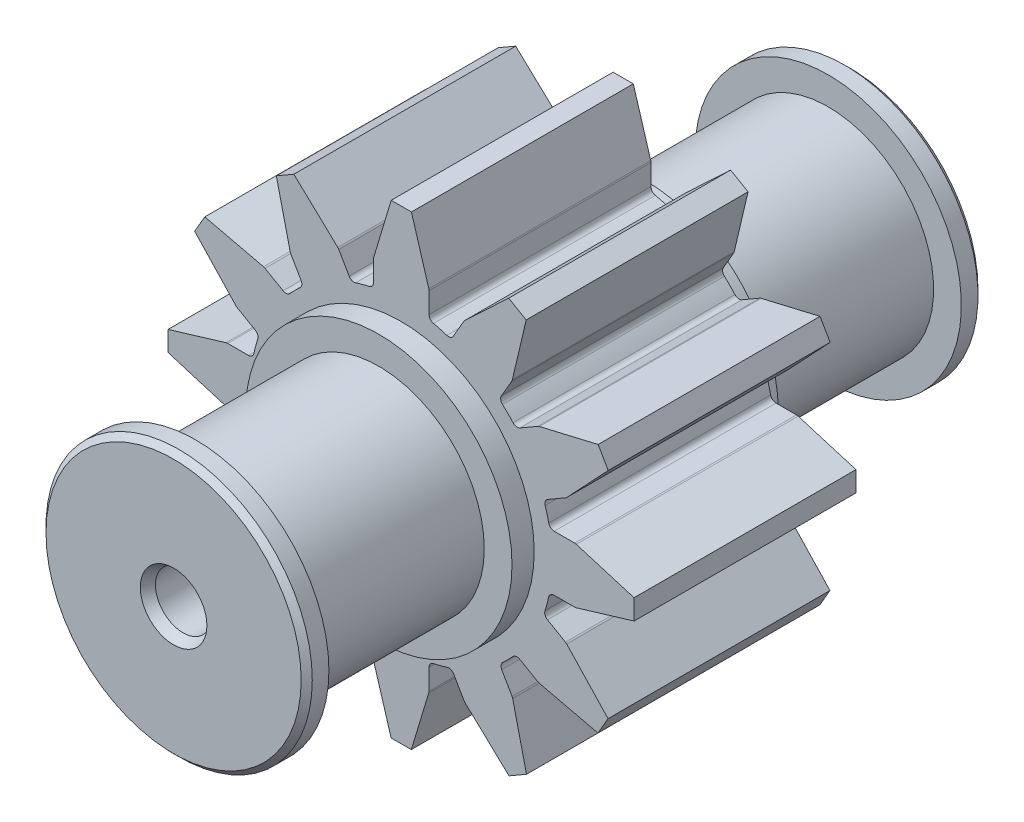
SolidWorks part; units mm, degrees
ref_plane "Спереди" through (0, 0, 0) normal (0, 0, 1) x (1, 0, 0)
ref_plane "Сверху" through (0, 0, 0) normal (0, 1, 0) x (1, 0, 0)
ref_plane "Справа" through (0, 0, 0) normal (1, 0, 0) x (0, 0, -1)
sketch "Эскиз2" plane through (0, 0, 0) normal (0, 0, 1) x (1, 0, 0)
  line L20 (53.7645, -2.946) -> (53.7645, -1.0771)
  line L21 (53.7433, -0.9329) -> (52.1747, 4.2742)
  line L22 (52.1747, 4.2742) -> (50.3546, 4.2742)
  line L23 (50.3546, 4.2742) -> (48.7858, -0.9329)
  line L24 (48.7645, -1.0772) -> (48.7645, -2.9531)
  line L27 (48.7555, -30.4797) -> (48.7555, -32.3473)
  line L28 (48.7768, -32.4916) -> (50.3453, -37.6987)
  line L29 (50.3453, -37.6987) -> (52.1655, -37.6987)
  line L30 (52.1655, -37.6987) -> (53.7343, -32.4916)
  line L31 (53.7555, -32.3473) -> (53.7555, -30.4775)
  line L34 (37.4896, -14.2638) -> (35.6099, -14.2638)
  line L36 (30.2415, -15.8598) -> (30.2586, -17.6738)
  line L37 (30.2586, -17.6738) -> (35.4657, -19.2426)
  line L38 (35.6099, -19.2638) -> (37.5151, -19.2638)
  line L39 (30.2415, -15.8598) -> (35.4656, -14.2851)
  line L41 (65.0289, -19.2139) -> (66.8888, -19.2139)
  line L42 (67.033, -19.1927) -> (72.2401, -17.6241)
  line L43 (72.2401, -17.6241) -> (72.2401, -15.8039)
  line L44 (72.2401, -15.8039) -> (67.033, -14.2352)
  line L45 (66.8887, -14.2139) -> (65.0384, -14.2141)
  line L48 (46.564, -3.5408) -> (45.6287, -1.9209)
  line L49 (45.5382, -1.8066) -> (41.5762, 1.9187)
  line L50 (41.5762, 1.9187) -> (39.9999, 1.0086)
  line L51 (39.9999, 1.0086) -> (41.2449, -4.2853)
  line L52 (41.2986, -4.4209) -> (42.233, -6.0394)
  line L55 (40.6086, -7.6603) -> (38.9805, -6.7203)
  line L56 (38.845, -6.6666) -> (33.5512, -5.4215)
  line L57 (33.5512, -5.4215) -> (32.6411, -6.9978)
  line L58 (32.6411, -6.9978) -> (36.3662, -10.9599)
  line L59 (36.4805, -11.0505) -> (38.0992, -11.985)
  line L62 (38.0961, -21.4251) -> (36.4775, -22.3596)
  line L63 (36.3633, -22.4501) -> (32.638, -26.4121)
  line L64 (32.638, -26.4121) -> (33.5481, -27.9884)
  line L65 (33.5481, -27.9884) -> (38.8378, -26.7444)
  line L66 (38.9806, -26.6864) -> (40.5573, -25.7405)
  line L67 (32.638, -26.4121) -> (36.4137, -22.3964)
  line L69 (42.2473, -27.4181) -> (41.3131, -29.0361)
  line L70 (41.2594, -29.1716) -> (40.0143, -34.4654)
  line L71 (40.0143, -34.4654) -> (41.5906, -35.3755)
  line L72 (41.5906, -35.3755) -> (45.553, -31.6502)
  line L73 (45.6432, -31.5364) -> (46.5897, -29.9013)
  line L76 (55.9807, -29.8805) -> (56.9183, -31.5045)
  line L77 (57.0088, -31.6188) -> (60.9708, -35.344)
  line L78 (60.9708, -35.344) -> (62.5471, -34.434)
  line L79 (62.5471, -34.434) -> (61.3021, -29.1401)
  line L80 (61.2484, -29.0045) -> (60.3134, -27.3849)
  line L83 (61.9386, -25.7577) -> (63.5568, -26.6919)
  line L84 (63.6923, -26.7456) -> (68.9861, -27.9908)
  line L85 (68.9861, -27.9908) -> (69.8962, -26.4145)
  line L86 (69.8962, -26.4145) -> (66.171, -22.4523)
  line L87 (66.0568, -22.3618) -> (64.4371, -21.4267)
  line L90 (64.4528, -12.024) -> (66.0728, -11.0887)
  line L91 (66.1871, -10.9982) -> (69.9123, -7.0362)
  line L92 (69.9123, -7.0362) -> (69.0022, -5.4599)
  line L93 (69.0022, -5.4599) -> (63.7083, -6.7049)
  line L94 (63.5728, -6.7586) -> (61.9545, -7.6929)
  line L97 (60.2872, -6.0251) -> (61.2186, -4.412)
  line L98 (61.2723, -4.2764) -> (62.5174, 1.0174)
  line L99 (62.5174, 1.0174) -> (60.9411, 1.9274)
  line L100 (60.9411, 1.9274) -> (56.979, -1.7977)
  line L101 (56.8884, -1.912) -> (55.9532, -3.5318)
  arc A0 (48.3706, -3.4418) -> (48.7645, -2.9531) centre (48.2645, -2.9531) ccw
  arc A1 (47.1481, -3.7675) -> (46.564, -3.5408) centre (46.997, -3.2908) cw
  arc A2 (48.3706, -3.4418) -> (47.1481, -3.7675) centre (51.2539, -16.7205) ccw
  arc A3 (54.1578, -3.4345) -> (55.3689, -3.7584) centre (51.2539, -16.7205) cw
  arc A4 (60.3845, -6.6456) -> (61.3338, -7.5955) centre (51.2539, -16.7205) cw
  arc A5 (64.2262, -12.6081) -> (64.5499, -13.8206) centre (51.2539, -16.7205) cw
  arc A6 (64.5403, -19.6077) -> (64.2107, -20.8421) centre (51.2539, -16.7205) cw
  arc A7 (61.3184, -25.8547) -> (60.4095, -26.7654) centre (51.2539, -16.7205) cw
  arc A8 (55.3952, -29.6543) -> (54.1489, -29.989) centre (51.2539, -16.7205) cw
  arc A9 (48.362, -29.9912) -> (47.1727, -29.6749) centre (51.2539, -16.7205) cw
  arc A10 (42.1495, -26.7971) -> (41.1853, -25.8337) centre (51.2539, -16.7205) cw
  arc A11 (38.3225, -20.8403) -> (38.0033, -19.6557) centre (51.2539, -16.7205) cw
  arc A12 (37.9785, -13.8689) -> (38.3253, -12.5708) centre (51.2539, -16.7205) cw
  arc A13 (41.2278, -7.5645) -> (42.1358, -6.6599) centre (51.2539, -16.7205) cw
  arc A14 (54.1578, -3.4345) -> (53.7645, -2.946) centre (54.2645, -2.946) cw
  arc A15 (55.3689, -3.7584) -> (55.9532, -3.5318) centre (55.5202, -3.2818) ccw
  arc A16 (60.3845, -6.6456) -> (60.2872, -6.0251) centre (60.7202, -6.2751) cw
  arc A17 (61.9545, -7.6929) -> (61.3338, -7.5955) centre (61.7045, -7.2599) cw
  arc A18 (56.979, -1.7977) -> (56.8884, -1.912) centre (57.3215, -2.162) ccw
  arc A19 (53.7433, -0.9329) -> (53.7645, -1.0771) centre (53.2645, -1.0771) cw
  arc A20 (48.7858, -0.9329) -> (48.7645, -1.0772) centre (49.2645, -1.0772) ccw
  arc A21 (45.5382, -1.8066) -> (45.6287, -1.9209) centre (45.1957, -2.1709) cw
  arc A22 (63.5728, -6.7586) -> (63.7083, -6.7049) centre (63.8228, -7.1916) cw
  arc A23 (61.2723, -4.2764) -> (61.2186, -4.412) centre (60.7856, -4.162) cw
  arc A24 (64.5499, -13.8206) -> (65.0384, -14.2141) centre (65.0384, -13.7141) ccw
  arc A25 (64.2262, -12.6081) -> (64.4528, -12.024) centre (64.7028, -12.457) cw
  arc A26 (66.8887, -14.2139) -> (67.033, -14.2352) centre (66.8888, -14.7139) cw
  arc A27 (66.1871, -10.9982) -> (66.0728, -11.0887) centre (65.8228, -10.6557) cw
  arc A28 (64.5403, -19.6077) -> (65.0289, -19.2139) centre (65.0289, -19.7139) cw
  arc A29 (67.033, -19.1927) -> (66.8888, -19.2139) centre (66.8888, -18.7139) cw
  arc A30 (64.4371, -21.4267) -> (64.2107, -20.8421) centre (64.6871, -20.9937) cw
  arc A31 (66.171, -22.4523) -> (66.0568, -22.3618) centre (65.8068, -22.7948) ccw
  arc A32 (61.3184, -25.8547) -> (61.9386, -25.7577) centre (61.6886, -26.1907) cw
  arc A33 (63.6923, -26.7456) -> (63.5568, -26.6919) centre (63.8068, -26.2589) cw
  arc A34 (60.3134, -27.3849) -> (60.4095, -26.7654) centre (60.7464, -27.1349) cw
  arc A35 (61.3021, -29.1401) -> (61.2484, -29.0045) centre (60.8154, -29.2545) ccw
  arc A36 (56.9183, -31.5045) -> (57.0088, -31.6188) centre (57.3513, -31.2545) ccw
  arc A37 (55.9807, -29.8805) -> (55.3952, -29.6543) centre (55.5477, -30.1305) ccw
  arc A38 (53.7555, -30.4775) -> (54.1489, -29.989) centre (54.2555, -30.4775) cw
  arc A39 (53.7343, -32.4916) -> (53.7555, -32.3473) centre (53.2555, -32.3473) ccw
  arc A40 (48.7555, -32.3473) -> (48.7768, -32.4916) centre (49.2555, -32.3473) ccw
  arc A41 (48.362, -29.9912) -> (48.7555, -30.4797) centre (48.2555, -30.4797) cw
  arc A42 (46.5897, -29.9013) -> (47.1727, -29.6749) centre (47.0224, -30.1518) cw
  arc A43 (45.553, -31.6502) -> (45.6432, -31.5364) centre (45.2105, -31.2859) ccw
  arc A44 (41.3131, -29.0361) -> (41.2594, -29.1716) centre (41.7462, -29.2861) ccw
  arc A45 (42.1495, -26.7971) -> (42.2473, -27.4181) centre (41.8143, -27.1681) cw
  arc A46 (41.1853, -25.8337) -> (40.5573, -25.7405) centre (40.8145, -26.1692) ccw
  arc A47 (38.8378, -26.7444) -> (38.9806, -26.6864) centre (38.7234, -26.2577) ccw
  arc A48 (36.4775, -22.3596) -> (36.3633, -22.4501) centre (36.7275, -22.7926) ccw
  arc A49 (38.0961, -21.4251) -> (38.3225, -20.8403) centre (37.8461, -20.9921) ccw
  arc A50 (37.5151, -19.2638) -> (38.0033, -19.6557) centre (37.5151, -19.7638) cw
  arc A51 (35.4657, -19.2426) -> (35.6099, -19.2638) centre (35.6099, -18.7638) ccw
  arc A52 (35.4656, -14.2851) -> (35.6099, -14.2638) centre (35.6099, -14.7638) cw
  arc A53 (37.9785, -13.8689) -> (37.4896, -14.2638) centre (37.4896, -13.7638) cw
  arc A54 (38.0992, -11.985) -> (38.3253, -12.5708) centre (37.8492, -12.418) cw
  arc A55 (36.3662, -10.9599) -> (36.4805, -11.0505) centre (36.7305, -10.6175) ccw
  arc A56 (38.9805, -6.7203) -> (38.845, -6.6666) centre (38.7305, -7.1534) ccw
  arc A57 (41.2278, -7.5645) -> (40.6086, -7.6603) centre (40.8586, -7.2273) cw
  arc A58 (42.233, -6.0394) -> (42.1358, -6.6599) centre (41.8, -6.2894) cw
  arc A59 (41.2449, -4.2853) -> (41.2986, -4.4209) centre (41.7316, -4.1709) ccw
extrude "Вытянуть1" add sketch "Эскиз2" along normal blind 20 contours L63 A48 L62 A49 A11 A50 L38 A51 L37 L36 L39 A52 L34 A53 A12 A54 L59 A55 L58 L57 L56 A56 L55 A57 A13 A58 L52 A59 L51 L50 L49 A21 L48 A1 A2 A0 L24 A20 L23 L22 L21 A19 L20 A14 A3 A15 L101 A18 L100 L99 L98 A23 L97 A16 A4 A17 L94 A22 L93 L92 L91 A27 L90 A25 A5 A24 L45 A26 L44 L43 L42 A29 L41 A28 A6 A30 L87 A31 L86 L85 L84 A33 L83 A32 A7 A34 L80 A35 L79 L78 L77 A36 L76 A37 A8 A38 L31 A39 L30 L29 L28 A40 L27 A41 A9 A42 L73 A43 L72 L71 L70 A44 L69 A45 A10 A46 L66 A47 L65 L64
sketch "Эскиз3" plane through (0, 0, 0) normal (0, 0, -1) x (-1, 0, 0)
  line L0 (-72.2401, -17.6241) -> (-72.2401, -15.8039) construction
  line L1 (-30.2415, -15.8598) -> (-30.2586, -17.6738) construction
  circle A0 centre (-51.2401, -16.7331) radius 12
  point P2 (-72.2401, -16.714)
  point P7 (-72.2401, -16.714)
  dimension "D1" = 41.9887
  dimension "D2" = 21
extrude "Вытянуть2" add sketch "Эскиз3" along normal blind 2
sketch "Эскиз4" plane through (0, 0, 20) normal (0, 0, 1) x (1, 0, 0)
  circle A0 centre (51.2401, -16.7331) radius 12
extrude "Вытянуть3" add sketch "Эскиз4" along normal blind 2
sketch "Эскиз5" plane through (0, 0, -2) normal (0, 0, -1) x (-1, 0, 0)
  circle A0 centre (-51.2401, -16.7331) radius 9.5
extrude "Вытянуть4" add sketch "Эскиз5" along normal blind 16.5
sketch "Эскиз6" plane through (0, 0, -18.5) normal (0, 0, -1) x (-1, 0, 0)
  circle A0 centre (-51.2401, -16.7331) radius 12
extrude "Вытянуть5" add sketch "Эскиз6" along normal blind 2
chamfer "Фаска2" distance 0.5 angle 45 1 edges at (39.2401, -16.7331, -20.5)
sketch "Эскиз7" plane through (0, 0, 22) normal (0, 0, 1) x (1, 0, 0)
  circle A0 centre (51.2401, -16.7331) radius 9.5
extrude "Вытянуть6" add sketch "Эскиз7" along normal blind 16.5
sketch "Эскиз8" plane through (0, 0, 38.5) normal (0, 0, 1) x (1, 0, 0)
  circle A0 centre (51.2401, -16.7331) radius 12
extrude "Вытянуть7" add sketch "Эскиз8" along normal blind 2
chamfer "Фаска3" distance 0.5 angle 45 1 edges at (63.2401, -16.7331, 40.5)
sketch "Эскиз15" plane through (0, 0, -20.5) normal (0, 0, -1) x (-1, 0, 0)
  circle A0 centre (-51.2401, -16.7331) radius 2.5
extrude "Вытянуть13" cut sketch "Эскиз15" against normal blind 74
chamfer "Фаска6" distance 0.5 angle 60 1 edges at (48.7401, -16.7331, -20.5)
chamfer "Фаска9" distance 0.5 angle 60 1 edges at (53.7401, -16.7331, 40.5)
